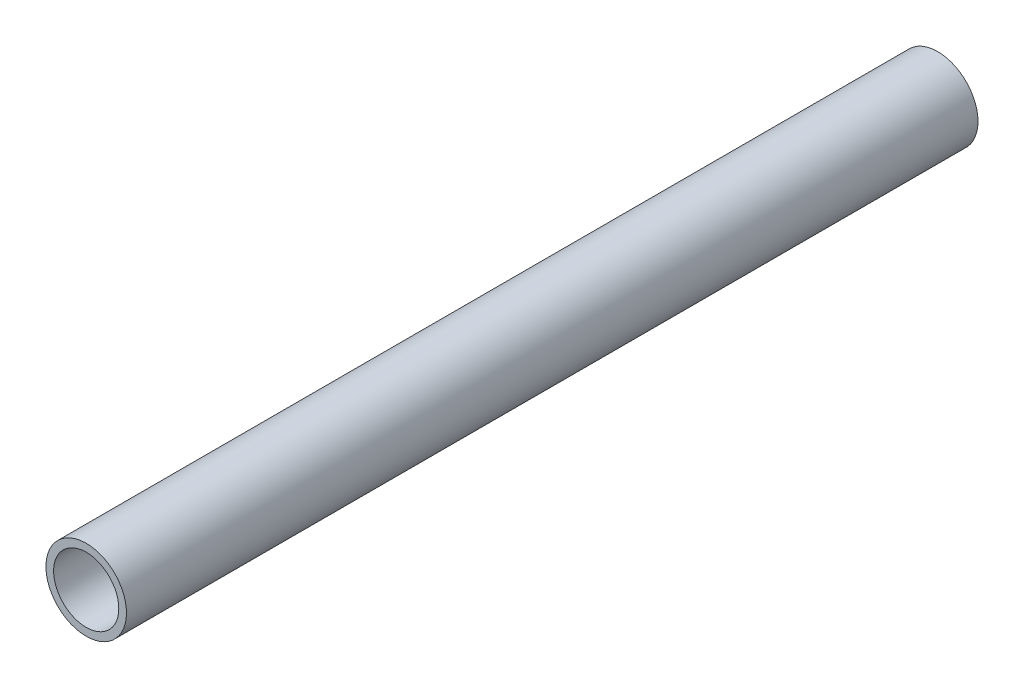
SolidWorks part; units mm, degrees
material "201.0-T43 Insulated Mold Casting (SS)"
ref_plane "Front Plane" through (0, 0, 0) normal (0, 0, 1) x (1, 0, 0)
ref_plane "Top Plane" through (0, 0, 0) normal (0, 1, 0) x (1, 0, 0)
ref_plane "Right Plane" through (0, 0, 0) normal (1, 0, 0) x (0, 0, -1)
sketch "Sketch1" plane through (0, 0, 0) normal (0, 0, 1) x (1, 0, 0)
  circle A0 centre (0, 0) radius 141.5
  circle A1 centre (0, 0) radius 175
  dimension "D1" = 283
  dimension "D2" = 350
extrude "Boss-Extrude1" add sketch "Sketch1" along normal mid plane 3700
